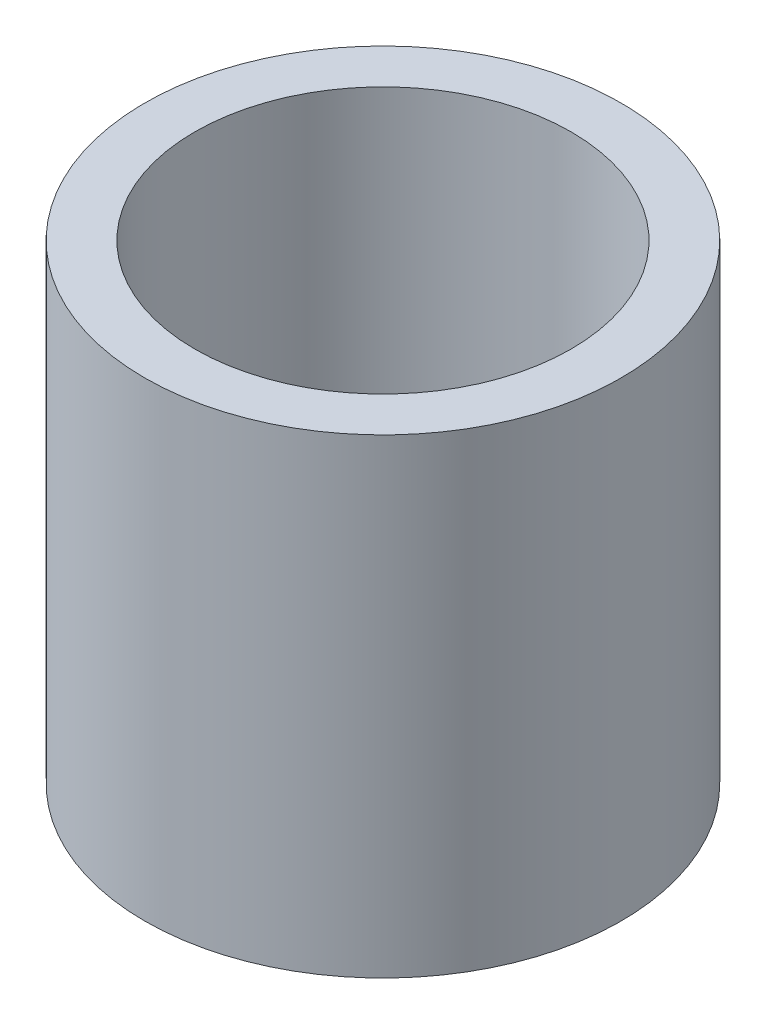
SolidWorks part; units mm, degrees
ref_plane "Front Plane" through (0, 0, 0) normal (0, 0, 1) x (1, 0, 0)
ref_plane "Top Plane" through (0, 0, 0) normal (0, 1, 0) x (1, 0, 0)
ref_plane "Right Plane" through (0, 0, 0) normal (1, 0, 0) x (0, 0, -1)
sketch "Sketch1" plane through (0, 0, 0) normal (0, 1, 0) x (1, 0, 0)
  circle A0 centre (0, 0) radius 7.9
  circle A1 centre (0, 0) radius 10
  dimension "D1" = 15.8
  dimension "D2" = 20
extrude "Boss-Extrude1" add sketch "Sketch1" along normal blind 19.75
equation "\"8mm hole\" = 8.4mm"
equation "\"22mm hole\"= 23mm"
equation "\"15mm hole\"= 15.8mm"
equation "\"D1@Sketch1\"= \"15mm hole\""
